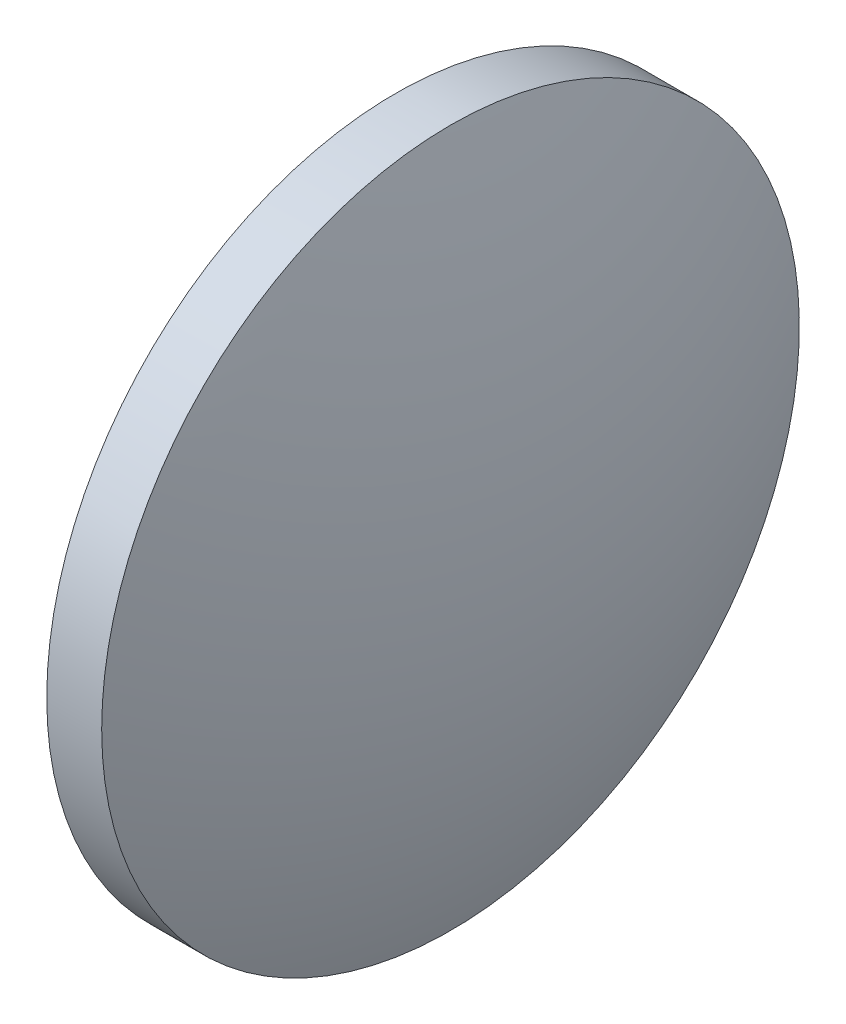
SolidWorks part; units mm, degrees
ref_plane "前视基准面" through (0, 0, 0) normal (0, 0, 1) x (1, 0, 0)
ref_plane "上视基准面" through (0, 0, 0) normal (0, 1, 0) x (1, 0, 0)
ref_plane "右视基准面" through (0, 0, 0) normal (1, 0, 0) x (0, 0, -1)
sketch "草图1" plane through (0, 0, 0) normal (0, 0, 1) x (1, 0, 0)
  line L0 (545.5036, 132.5932) -> (564.2996, 132.5932) construction
  line L1 (551.2083, 132.5932) -> (551.2083, 145.2932)
  line L2 (551.2083, 145.2932) -> (553.2083, 145.2932)
  line L3 (555.6483, 132.5932) -> (551.2083, 132.5932)
  arc A0 (555.6483, 132.5932) -> (553.2083, 145.2932) centre (521.377, 132.5932) ccw
revolve "旋转1" add sketch "草图1" angle 360 about L0
